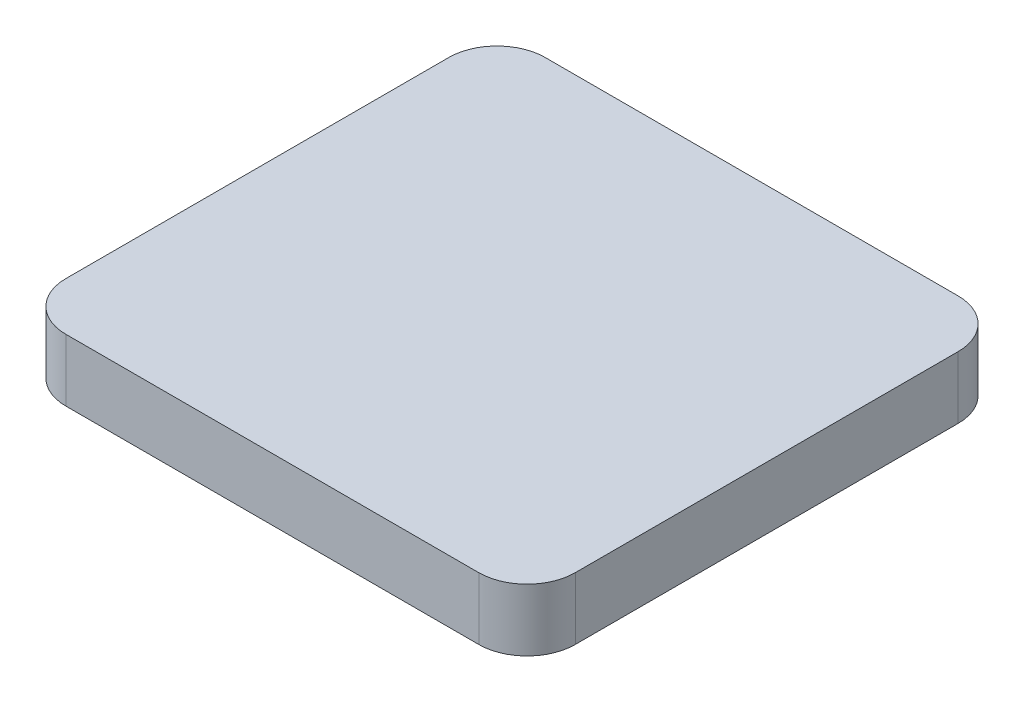
SolidWorks part; units mm, degrees
ref_plane "Front Plane" through (0, 0, 0) normal (0, 0, 1) x (1, 0, 0)
ref_plane "Top Plane" through (0, 0, 0) normal (0, 1, 0) x (1, 0, 0)
ref_plane "Right Plane" through (0, 0, 0) normal (1, 0, 0) x (0, 0, -1)
sketch "Sketch1" plane through (0, 0, 0) normal (0, 1, 0) x (1, 0, 0)
  line L0 (-21.75, 20.35) -> (-21.75, 22.35) construction
  line L1 (19.25, 20.35) -> (-19.25, 20.35)
  line L2 (21.75, 17.85) -> (21.75, -17.85)
  line L3 (19.25, -20.35) -> (-19.25, -20.35)
  line L4 (-21.75, 17.85) -> (-21.75, -17.85)
  line L5 (21.75, 20.35) -> (-21.75, -20.35) construction
  line L6 (21.75, -20.35) -> (-21.75, 20.35) construction
  line L7 (23.75, -22.35) -> (-23.75, -22.35)
  line L8 (23.75, -22.35) -> (23.75, 22.35)
  line L9 (23.75, 22.35) -> (-23.75, 22.35)
  line L10 (-23.75, -22.35) -> (-23.75, 22.35)
  line L11 (23.75, -22.35) -> (-23.75, 22.35) construction
  line L12 (23.75, 22.35) -> (-23.75, -22.35) construction
  line L13 (-21.75, 20.35) -> (-23.75, 20.35) construction
  arc A0 (-19.25, -20.35) -> (-21.75, -17.85) centre (-19.25, -17.85) cw
  arc A1 (21.75, -17.85) -> (19.25, -20.35) centre (19.25, -17.85) cw
  arc A2 (19.25, 20.35) -> (21.75, 17.85) centre (19.25, 17.85) cw
  arc A3 (-19.25, 20.35) -> (-21.75, 17.85) centre (-19.25, 17.85) ccw
  circle A4 centre (-19.25, 17.85) radius 4.5
  circle A5 centre (19.25, 17.85) radius 4.5
  circle A6 centre (19.25, -17.85) radius 4.5
  circle A7 centre (-19.25, -17.85) radius 4.5
  point P0 (0, 0)
  point P6 (0, 0)
  dimension "D4" = 2.5
  dimension "D1" = 43.5
  dimension "D2" = 40.7
  dimension "D3" = 2
extrude "Boss-Extrude1" add sketch "Sketch1" along normal blind 1.3 contours L1 A4 L4 A3 | A7 L4 A4 L10 | A7 L3 A0 L4 | A7 L7 A6 L3 | A6 L2 A1 L3 | A6 L8 A5 L2 | L2 A5 L1 A2 | A5 L9 A4 L1
sketch "Sketch2" plane through (0, 1.3, 0) normal (0, 1, 0) x (1, 0, 0)
  line L4 (-19.25, -22.35) -> (19.25, -22.35)
  line L5 (23.75, -17.85) -> (23.75, 17.85)
  line L6 (19.25, 22.35) -> (-19.25, 22.35)
  line L7 (-23.75, 17.85) -> (-23.75, -17.85)
  line L8 (-19.25, -22.35) -> (19.25, -22.35)
  line L9 (23.75, -17.85) -> (23.75, 17.85)
  line L10 (19.25, 22.35) -> (-19.25, 22.35)
  line L11 (-23.75, 17.85) -> (-23.75, -17.85)
  arc A4 (19.25, -22.35) -> (23.75, -17.85) centre (19.25, -17.85) ccw
  arc A5 (23.75, 17.85) -> (19.25, 22.35) centre (19.25, 17.85) ccw
  arc A6 (-19.25, 22.35) -> (-23.75, 17.85) centre (-19.25, 17.85) ccw
  arc A7 (-23.75, -17.85) -> (-19.25, -22.35) centre (-19.25, -17.85) ccw
  arc A8 (19.25, -22.35) -> (23.75, -17.85) centre (19.25, -17.85) ccw
  arc A9 (23.75, 17.85) -> (19.25, 22.35) centre (19.25, 17.85) ccw
  arc A10 (-19.25, 22.35) -> (-23.75, 17.85) centre (-19.25, 17.85) ccw
  arc A11 (-23.75, -17.85) -> (-19.25, -22.35) centre (-19.25, -17.85) ccw
  dimension "D1" = 0
extrude "Boss-Extrude2" add sketch "Sketch2" along normal blind 1.5
sketch "Sketch3" plane through (0, 1.3, 0) normal (0, -1, 0) x (1, 0, 0)
  line L0 (-23.75, 0) -> (23.75, 0) construction
  line L1 (-23.75, 17.85) -> (-23.75, -17.85) construction
  line L2 (23.75, 17.85) -> (23.75, -17.85) construction
  line L3 (-23.75, 11.175) -> (23.75, 11.175) construction
  line L4 (0, 11.175) -> (0, 22.35) construction
  line L5 (19.25, 22.35) -> (-19.25, 22.35) construction
  line L6 (0, 11.175) -> (0, 0) construction
  line L7 (-23.75, -11.175) -> (23.75, -11.175) construction
  line L8 (0, 0) -> (4.1348, 4.1348) construction
  line L9 (11.175, -23.75) -> (11.175, 23.75) construction
  line L10 (-11.175, -23.75) -> (-11.175, 23.75) construction
  line L11 (-21.75, -17.85) -> (-21.75, 17.85) construction
  line L12 (-21.75, -17.85) -> (-21.75, 17.85) construction
  line L13 (19.25, -20.35) -> (-19.25, -20.35) construction
  line L14 (21.75, -17.85) -> (21.75, 17.85) construction
  line L15 (19.25, 20.35) -> (-19.25, 20.35) construction
  line L16 (19.25, 20.35) -> (-19.25, 20.35) construction
  line L17 (0, 0) -> (0, -20.35) construction
  circle A0 centre (-21.75, 11.175) radius 0.4
  circle A1 centre (-21.75, 0) radius 0.4
  circle A2 centre (-21.75, -11.175) radius 0.4
  circle A3 centre (-11.175, -20.35) radius 0.4
  circle A4 centre (11.175, -20.35) radius 0.4
  circle A5 centre (21.75, -11.175) radius 0.4
  circle A6 centre (21.75, 0) radius 0.4
  circle A7 centre (21.75, 11.175) radius 0.4
  circle A8 centre (11.175, 20.35) radius 0.4
  circle A9 centre (0, 20.35) radius 0.4
  circle A10 centre (-11.175, 20.35) radius 0.4
  circle A11 centre (0, -20.35) radius 0.4
  dimension "D2" = 0.8
  dimension "D1" = 45
extrude "Boss-Extrude3" add sketch "Sketch3" along normal up to surface (1.3 mm away) up to face at (0, 0, 0)
sketch "Sketch4" plane through (0, 0, 0) normal (0, -1, 0) x (1, 0, 0)
  line L0 (-22.75, 17.85) -> (-22.75, -17.85)
  line L1 (-19.25, -21.35) -> (19.25, -21.35)
  line L2 (22.75, -17.85) -> (22.75, 17.85)
  line L3 (19.25, 21.35) -> (-19.25, 21.35)
  line L4 (19.25, 22.35) -> (-19.25, 22.35)
  line L5 (-23.75, 17.85) -> (-23.75, -17.85)
  line L6 (-19.25, -22.35) -> (19.25, -22.35)
  line L7 (23.75, -17.85) -> (23.75, 17.85)
  line L8 (19.25, 22.35) -> (-19.25, 22.35)
  line L9 (-23.75, 17.85) -> (-23.75, -17.85)
  line L10 (-19.25, -22.35) -> (19.25, -22.35)
  line L11 (23.75, -17.85) -> (23.75, 17.85)
  arc A0 (-19.25, 21.35) -> (-22.75, 17.85) centre (-19.25, 17.85) ccw
  arc A1 (-22.75, -17.85) -> (-19.25, -21.35) centre (-19.25, -17.85) ccw
  arc A2 (19.25, -21.35) -> (22.75, -17.85) centre (19.25, -17.85) ccw
  arc A3 (22.75, 17.85) -> (19.25, 21.35) centre (19.25, 17.85) ccw
  arc A4 (-19.25, 22.35) -> (-23.75, 17.85) centre (-19.25, 17.85) ccw
  arc A5 (-23.75, -17.85) -> (-19.25, -22.35) centre (-19.25, -17.85) ccw
  arc A6 (19.25, -22.35) -> (23.75, -17.85) centre (19.25, -17.85) ccw
  arc A7 (23.75, 17.85) -> (19.25, 22.35) centre (19.25, 17.85) ccw
  arc A8 (-19.25, 22.35) -> (-23.75, 17.85) centre (-19.25, 17.85) ccw
  arc A9 (-23.75, -17.85) -> (-19.25, -22.35) centre (-19.25, -17.85) ccw
  arc A10 (19.25, -22.35) -> (23.75, -17.85) centre (19.25, -17.85) ccw
  arc A11 (23.75, 17.85) -> (19.25, 22.35) centre (19.25, 17.85) ccw
  dimension "D1" = 0
  dimension "D2" = 1
extrude "Boss-Extrude4" add sketch "Sketch4" along normal blind 3
sketch "Sketch5" plane through (0, 1.3, 0) normal (0, -1, 0) x (1, 0, 0)
  line L16 (0.9798, -19.35) -> (10.1952, -19.35)
  line L17 (0.9798, -19.35) -> (10.1952, -19.35)
  line L31 (-12.1548, 19.35) -> (-19.25, 19.35)
  line L32 (-20.75, 17.85) -> (-20.75, 12.1548)
  line L33 (-20.75, 10.1952) -> (-20.75, 0.9798)
  line L34 (-20.75, -0.9798) -> (-20.75, -10.1952)
  line L35 (-20.75, -12.1548) -> (-20.75, -17.85)
  line L36 (-19.25, -19.35) -> (-12.1548, -19.35)
  line L37 (-10.1952, -19.35) -> (-0.9798, -19.35)
  line L38 (12.1548, -19.35) -> (19.25, -19.35)
  line L39 (20.75, -17.85) -> (20.75, -12.1548)
  line L40 (20.75, -10.1952) -> (20.75, -0.9798)
  line L41 (20.75, 0.9798) -> (20.75, 10.1952)
  line L42 (20.75, 12.1548) -> (20.75, 17.85)
  line L43 (19.25, 19.35) -> (12.1548, 19.35)
  line L44 (10.1952, 19.35) -> (0.9798, 19.35)
  line L45 (-0.9798, 19.35) -> (-10.1952, 19.35)
  line L46 (-12.1548, 19.35) -> (-19.25, 19.35)
  line L47 (-20.75, 17.85) -> (-20.75, 12.1548)
  line L48 (-20.75, 10.1952) -> (-20.75, 0.9798)
  line L49 (-20.75, -0.9798) -> (-20.75, -10.1952)
  line L50 (-20.75, -12.1548) -> (-20.75, -17.85)
  line L51 (-19.25, -19.35) -> (-12.1548, -19.35)
  line L52 (-10.1952, -19.35) -> (-0.9798, -19.35)
  line L53 (12.1548, -19.35) -> (19.25, -19.35)
  line L54 (20.75, -17.85) -> (20.75, -12.1548)
  line L55 (20.75, -10.1952) -> (20.75, -0.9798)
  line L56 (20.75, 0.9798) -> (20.75, 10.1952)
  line L57 (20.75, 12.1548) -> (20.75, 17.85)
  line L58 (19.25, 19.35) -> (12.1548, 19.35)
  line L59 (10.1952, 19.35) -> (0.9798, 19.35)
  line L60 (-0.9798, 19.35) -> (-10.1952, 19.35)
  arc A16 (0.9798, -19.35) -> (-0.9798, -19.35) centre (0, -20.35) ccw
  arc A17 (0.9798, -19.35) -> (-0.9798, -19.35) centre (0, -20.35) ccw
  arc A30 (-12.1548, 19.35) -> (-10.1952, 19.35) centre (-11.175, 20.35) ccw
  arc A31 (-19.25, 19.35) -> (-20.75, 17.85) centre (-19.25, 17.85) ccw
  arc A32 (-20.75, 10.1952) -> (-20.75, 12.1548) centre (-21.75, 11.175) ccw
  arc A33 (-20.75, -0.9798) -> (-20.75, 0.9798) centre (-21.75, 0) ccw
  arc A34 (-20.75, -12.1548) -> (-20.75, -10.1952) centre (-21.75, -11.175) ccw
  arc A35 (-20.75, -17.85) -> (-19.25, -19.35) centre (-19.25, -17.85) ccw
  arc A36 (-10.1952, -19.35) -> (-12.1548, -19.35) centre (-11.175, -20.35) ccw
  arc A37 (12.1548, -19.35) -> (10.1952, -19.35) centre (11.175, -20.35) ccw
  arc A38 (19.25, -19.35) -> (20.75, -17.85) centre (19.25, -17.85) ccw
  arc A39 (20.75, -10.1952) -> (20.75, -12.1548) centre (21.75, -11.175) ccw
  arc A40 (20.75, 0.9798) -> (20.75, -0.9798) centre (21.75, 0) ccw
  arc A41 (20.75, 12.1548) -> (20.75, 10.1952) centre (21.75, 11.175) ccw
  arc A42 (20.75, 17.85) -> (19.25, 19.35) centre (19.25, 17.85) ccw
  arc A43 (10.1952, 19.35) -> (12.1548, 19.35) centre (11.175, 20.35) ccw
  arc A44 (-0.9798, 19.35) -> (0.9798, 19.35) centre (0, 20.35) ccw
  arc A45 (-12.1548, 19.35) -> (-10.1952, 19.35) centre (-11.175, 20.35) ccw
  arc A46 (-19.25, 19.35) -> (-20.75, 17.85) centre (-19.25, 17.85) ccw
  arc A47 (-20.75, 10.1952) -> (-20.75, 12.1548) centre (-21.75, 11.175) ccw
  arc A48 (-20.75, -0.9798) -> (-20.75, 0.9798) centre (-21.75, 0) ccw
  arc A49 (-20.75, -12.1548) -> (-20.75, -10.1952) centre (-21.75, -11.175) ccw
  arc A50 (-20.75, -17.85) -> (-19.25, -19.35) centre (-19.25, -17.85) ccw
  arc A51 (-10.1952, -19.35) -> (-12.1548, -19.35) centre (-11.175, -20.35) ccw
  arc A52 (12.1548, -19.35) -> (10.1952, -19.35) centre (11.175, -20.35) ccw
  arc A53 (19.25, -19.35) -> (20.75, -17.85) centre (19.25, -17.85) ccw
  arc A54 (20.75, -10.1952) -> (20.75, -12.1548) centre (21.75, -11.175) ccw
  arc A55 (20.75, 0.9798) -> (20.75, -0.9798) centre (21.75, 0) ccw
  arc A56 (20.75, 12.1548) -> (20.75, 10.1952) centre (21.75, 11.175) ccw
  arc A57 (20.75, 17.85) -> (19.25, 19.35) centre (19.25, 17.85) ccw
  arc A58 (10.1952, 19.35) -> (12.1548, 19.35) centre (11.175, 20.35) ccw
  arc A59 (-0.9798, 19.35) -> (0.9798, 19.35) centre (0, 20.35) ccw
  dimension "D1" = 1
extrude "Cut-Extrude1" cut sketch "Sketch5" against normal blind 0.5
sketch "Sketch8" plane through (0, 0, 0) normal (0, -1, 0) x (1, 0, 0)
  line L0 (-11.175, 20.35) -> (-11.175, -20.35) construction
  line L1 (0, -20.35) -> (0, 20.35) construction
  line L2 (11.175, 20.35) -> (11.175, -20.35) construction
  line L3 (-21.75, 11.175) -> (21.75, 11.175) construction
  line L4 (21.75, 0) -> (-21.75, 0) construction
  line L5 (-21.75, -11.175) -> (21.75, -11.175) construction
  line L6 (19.25, 21.35) -> (-19.25, 21.35) construction
  line L7 (22.75, -17.85) -> (22.75, 17.85) construction
  line L8 (22.75, -17.85) -> (22.75, 17.85) construction
  line L9 (-19.25, -21.35) -> (19.25, -21.35) construction
  line L10 (-22.75, 17.85) -> (-22.75, -17.85) construction
  line L11 (-22.75, 17.85) -> (-22.75, -17.85) construction
  circle A0 centre (-11.175, 21.35) radius 0.4
  arc A1 (-11.575, 20.35) -> (-10.775, 20.35) centre (-11.175, 20.35) ccw construction
  circle A2 centre (0, 21.35) radius 0.4
  circle A3 centre (11.175, 21.35) radius 0.4
  circle A4 centre (22.75, 11.175) radius 0.4
  circle A5 centre (-22.75, 11.175) radius 0.4
  circle A6 centre (-22.75, 0) radius 0.4
  circle A7 centre (22.75, 0) radius 0.4
  circle A8 centre (22.75, -11.175) radius 0.4
  circle A9 centre (11.175, -21.35) radius 0.4
  circle A10 centre (0, -21.35) radius 0.4
  circle A11 centre (-11.175, -21.35) radius 0.4
  circle A12 centre (-22.75, -11.175) radius 0.4
  point P53 (0, 21)
  point P54 (11, 21)
  point P55 (22.9, 11)
  point P58 (22.9, 0)
  point P59 (22.9, -11)
  point P62 (11, -21)
  point P65 (0, -21)
  point P66 (-11, -21)
  point P67 (-11, -21)
  point P68 (-22.9, -11)
  point P71 (-22.9, 0)
  point P72 (-22.9, 11)
  point P73 (-22.9, 11)
extrude "Boss-Extrude5" add sketch "Sketch8" along normal up to surface (3 mm away) up to face at (0, -3, 0)
